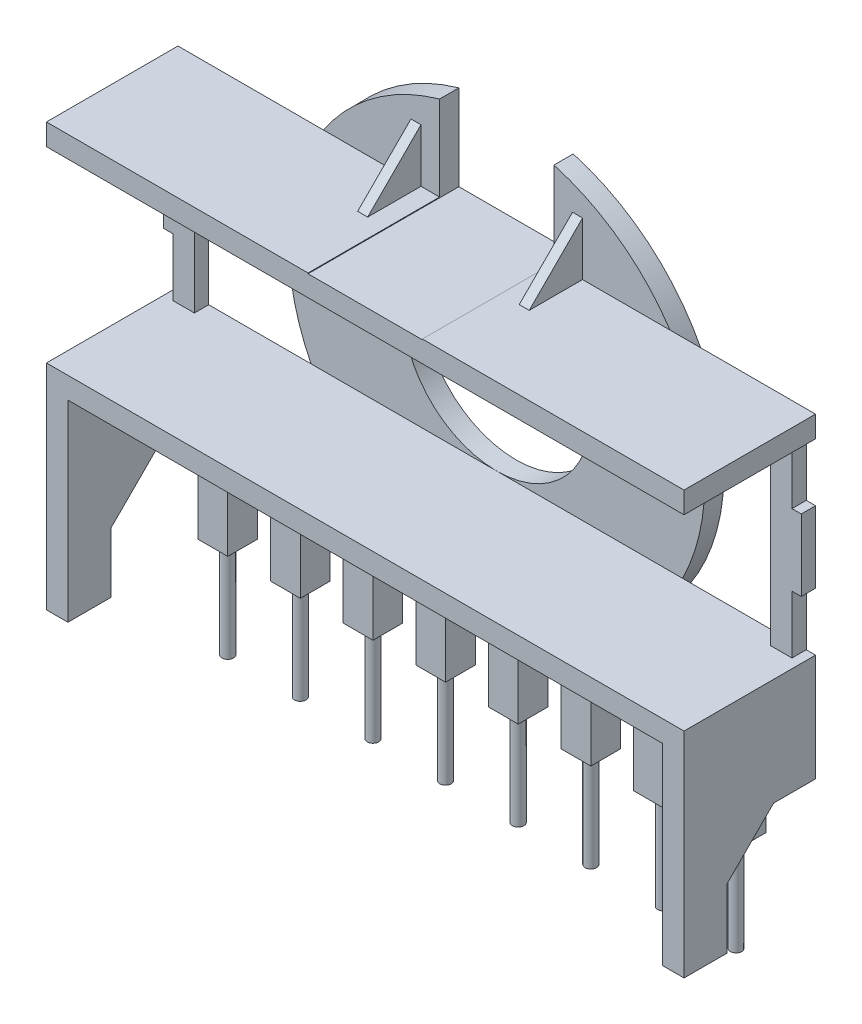
SolidWorks part; units mm, degrees
ref_plane "Front Plane" through (0, 0, 0) normal (0, 0, 1) x (1, 0, 0)
ref_plane "Top Plane" through (0, 0, 0) normal (0, 1, 0) x (1, 0, 0)
ref_plane "Right Plane" through (0, 0, 0) normal (1, 0, 0) x (0, 0, -1)
sketch "Sketch1" plane through (0, 0, 0) normal (0, 0, 1) x (1, 0, 0)
  line L0 (-4, 8) -> (0, 8)
  line L1 (0, 8) -> (4, 8)
  line L2 (4, 8) -> (4, 13.9894)
  line L3 (-4, 8) -> (-4, 13.9894)
  circle A0 centre (0, 0) radius 14.55
  circle A1 centre (0, 0) radius 6.55
  dimension "D1" = 29.1
  dimension "D2" = 13.1
  dimension "D3" = 8
  dimension "D4" = 8
extrude "Boss-Extrude1" add sketch "Sketch1" along normal blind 1.35 contours L3 A0 L2 L1 L0 A1
sketch "Sketch2" plane through (0, 0, 1.35) normal (0, 0, 1) x (1, 0, 0)
  line L1 (-22.3, 8.05) -> (22.3, 8.05)
  line L2 (-22.3, 8.05) -> (-22.3, 6.55)
  line L3 (-22.3, 6.55) -> (22.3, 6.55)
  line L4 (22.3, 8.05) -> (22.3, 6.55)
  line L5 (-22.3, 8.05) -> (22.3, 6.55) construction
  line L6 (-22.3, 6.55) -> (22.3, 8.05) construction
  line L7 (-22.3, -6.55) -> (22.3, -6.55)
  line L8 (-22.3, -6.55) -> (-22.3, -8.05)
  line L9 (-22.3, -8.05) -> (22.3, -8.05)
  line L10 (22.3, -6.55) -> (22.3, -8.05)
  line L11 (-22.3, -6.55) -> (22.3, -8.05) construction
  line L12 (-22.3, -8.05) -> (22.3, -6.55) construction
  line L13 (22.3, -8.05) -> (20.8, -8.05)
  line L14 (22.3, -8.05) -> (22.3, -21.5106)
  line L15 (22.3, -21.5106) -> (20.8, -21.5106)
  line L16 (20.8, -8.05) -> (20.8, -21.5106)
  line L17 (-22.3, -8.05) -> (-20.8, -8.05)
  line L18 (-22.3, -8.05) -> (-22.3, -21.5106)
  line L19 (-22.3, -21.5106) -> (-20.8, -21.5106)
  line L20 (-20.8, -8.05) -> (-20.8, -21.5106)
  line L21 (-5.3, 8.05) -> (-6, 8.05)
  line L22 (-5.3, 8.05) -> (-5.3, 11.7809)
  line L23 (-5.3, 11.7809) -> (-6, 11.7809)
  line L24 (-6, 8.05) -> (-6, 11.7809)
  line L25 (5.3, 8.05) -> (6, 8.05)
  line L26 (5.3, 8.05) -> (5.3, 11.7809)
  line L27 (5.3, 11.7809) -> (6, 11.7809)
  line L28 (6, 8.05) -> (6, 11.7809)
  circle A1 centre (0, 0) radius 6.55 construction
  point P0 (0, 7.3)
  point P5 (0, -7.3)
  line M2 (-4, 8) -> (-4, 13.9894)
  arc M3 (-4, 13.9894) -> (4, 13.9894) centre (0, 0) ccw
  line M4 (4, 13.9894) -> (4, 8)
  line M5 (4, 8) -> (-4, 8)
  dimension "D1" = 44.6
  dimension "D2" = 1.5
  dimension "D3" = 1.5
  dimension "D4" = 1.5
  dimension "D5" = 6
  dimension "D6" = 0.7
  dimension "D7" = 6
  dimension "D8" = 35.5
extrude "Boss-Extrude2" add sketch "Sketch2" along normal blind 9.2 contours L4 L1 L3 M3 | L1 L28 L27 L26 | L3 L1 M3 M4 M5 M2 | L2 L3 L1 M3 | L20 L9 L18 L19 | L8 L9 L7 M3 | L9 L7 M3 | L10 L7 L9 M3 | L14 L15 L16 L13 | L24 L23 L22 L21
sketch "Sketch3" plane through (0, 0, 1.35) normal (0, 0, 1) x (1, 0, 0)
  line L0 (-20.15, 6.55) -> (-20.15, -6.55)
  line L1 (-22.3, 6.55) -> (22.3, 6.55) construction
  line L2 (-22.3, -6.55) -> (22.3, -6.55) construction
  line L3 (21.65, 6.55) -> (21.65, -6.55)
  line L4 (-21.65, 6.55) -> (-21.65, -6.55)
  line L5 (20.15, 6.55) -> (20.15, -6.55)
  line L6 (-21.65, 6.55) -> (-20.15, 6.55)
  line L7 (20.15, 6.55) -> (21.65, 6.55)
  line L8 (20.15, -6.55) -> (21.65, -6.55)
  line L9 (-21.65, -6.55) -> (-20.15, -6.55)
  line L10 (-22.3, 2.5) -> (-22.3, -2.5)
  line L11 (22.3, 2.5) -> (22.3, -2.5)
  line L12 (-22.3, 2.5) -> (-21.65, 2.5)
  line L13 (-22.3, -2.5) -> (-21.65, -2.5)
  line L14 (22.3, 2.5) -> (21.65, 2.5)
  line L15 (22.3, -2.5) -> (21.65, -2.5)
  dimension "D1" = 40.3
  dimension "D2" = 20.15
  dimension "D3" = 1.5
  dimension "D4" = 1.5
  dimension "D5" = 44.6
  dimension "D6" = 22.3
  dimension "D7" = 5
  dimension "D8" = 2.5
  dimension "D9" = 5
extrude "Boss-Extrude3" add sketch "Sketch3" along normal blind 1 contours L4 L9 L0 L6 | L10 L13 L4 L12 | L15 L11 L14 L3 | L5 L8 L3 L7
sketch "Sketch5" plane through (6, 0, 0) normal (1, 0, 0) x (0, 0, -1)
  line L0 (-10.55, 8.05) -> (-5.0809, 8.05)
  line L1 (-10.55, 8.05) -> (-1.35, 8.05) construction
  line L2 (-5.0809, 8.05) -> (-1.35, 11.7809)
  line L3 (-1.35, 11.7809) -> (-10.55, 11.7809)
  line L4 (-10.55, 11.7809) -> (-10.55, 8.05)
  line L5 (-1.35, 8.05) -> (-1.35, 11.7809) construction
  dimension "D1" = 45
extrude "Cut-Extrude1" cut sketch "Sketch5" against normal through all
sketch "Sketch6" plane through (22.3, 0, 0) normal (1, 0, 0) x (0, 0, -1)
  line L0 (-7.55, -21.5106) -> (-7.55, -17.3175)
  line L1 (-10.55, -21.5106) -> (-1.35, -21.5106) construction
  line L2 (-7.55, -17.3175) -> (-4.2825, -14.05)
  line L3 (-4.2825, -14.05) -> (-1.35, -14.05)
  line L4 (-1.35, -6.55) -> (-1.35, -21.5106) construction
  line L5 (-1.35, -14.05) -> (-1.35, -21.5106)
  line L6 (-1.35, -21.5106) -> (-7.55, -21.5106)
  line L7 (-10.55, -6.55) -> (-1.35, -6.55) construction
  line L8 (-10.55, -6.55) -> (-10.55, -21.5106) construction
  dimension "D1" = 135
  dimension "D2" = 7.5
  dimension "D3" = 3
extrude "Cut-Extrude2" cut sketch "Sketch6" against normal through all
sketch "Sketch7" plane through (0, 0, 1.35) normal (0, 0, 1) x (1, 0, 0)
  line L1 (-20.8, -8.05) -> (20.8, -8.05)
  line L2 (-20.8, -8.05) -> (-20.8, -15.05)
  line L3 (-20.8, -15.05) -> (20.8, -15.05)
  line L4 (20.8, -8.05) -> (20.8, -15.05)
  dimension "D1" = 7
  dimension "D2" = 20.8
extrude "Boss-Extrude4" add sketch "Sketch7" along normal blind 0.5
sketch "Sketch8" plane through (0, -15.05, 0) normal (0, -1, 0) x (1, 0, 0)
  circle A0 centre (-17.78, 2.39) radius 0.4
  circle A1 centre (-12.7, 2.39) radius 0.4
  circle A2 centre (-7.62, 2.39) radius 0.4
  circle A3 centre (-2.54, 2.39) radius 0.4
  circle A4 centre (2.54, 2.39) radius 0.4
  circle A5 centre (7.62, 2.39) radius 0.4
  circle A6 centre (12.7, 2.39) radius 0.4
  circle A7 centre (17.78, 2.39) radius 0.4
  dimension "D2" = 0.8
  dimension "D1" = 2.39
  dimension "D3" = 2.54
  dimension "D4" = 5.08
  dimension "D5" = 5.08
  dimension "D6" = 5.08
  dimension "D7" = 5.08
  dimension "D8" = 5.08
  dimension "D9" = 5.08
  dimension "D10" = 5.08
extrude "Pins" add sketch "Sketch8" along normal blind 11 separate body
sketch "Sketch9" plane through (0, -8.05, 0) normal (0, -1, 0) x (1, 0, 0)
  line L0 (-12.9923, 1.35) -> (12.9923, 1.35) construction
  line L1 (-13.74, 3.43) -> (-11.66, 3.43)
  line L2 (-13.74, 3.43) -> (-13.74, 1.35)
  line L3 (-13.74, 1.35) -> (-11.66, 1.35)
  line L4 (-11.66, 3.43) -> (-11.66, 1.35)
  line L5 (-13.74, 3.43) -> (-11.66, 1.35) construction
  line L6 (-13.74, 1.35) -> (-11.66, 3.43) construction
  line L7 (-20.8, 1.35) -> (20.8, 1.35) construction
  line L8 (-18.82, 3.43) -> (-16.74, 3.43)
  line L9 (-18.82, 3.43) -> (-18.82, 1.35)
  line L10 (-18.82, 1.35) -> (-16.74, 1.35)
  line L11 (-16.74, 3.43) -> (-16.74, 1.35)
  line L12 (-18.82, 3.43) -> (-16.74, 1.35) construction
  line L13 (-18.82, 1.35) -> (-16.74, 3.43) construction
  line L15 (-8.66, 3.43) -> (-6.58, 3.43)
  line L16 (-8.66, 3.43) -> (-8.66, 1.35)
  line L17 (-8.66, 1.35) -> (-6.58, 1.35)
  line L18 (-6.58, 3.43) -> (-6.58, 1.35)
  line L19 (-8.66, 3.43) -> (-6.58, 1.35) construction
  line L20 (-8.66, 1.35) -> (-6.58, 3.43) construction
  line L21 (-3.58, 3.43) -> (-1.5, 3.43)
  line L22 (-3.58, 3.43) -> (-3.58, 1.35)
  line L23 (-3.58, 1.35) -> (-1.5, 1.35)
  line L24 (-1.5, 3.43) -> (-1.5, 1.35)
  line L25 (-3.58, 3.43) -> (-1.5, 1.35) construction
  line L26 (-3.58, 1.35) -> (-1.5, 3.43) construction
  line L27 (1.5, 3.43) -> (3.58, 3.43)
  line L28 (1.5, 3.43) -> (1.5, 1.35)
  line L29 (1.5, 1.35) -> (3.58, 1.35)
  line L30 (3.58, 3.43) -> (3.58, 1.35)
  line L31 (1.5, 3.43) -> (3.58, 1.35) construction
  line L32 (1.5, 1.35) -> (3.58, 3.43) construction
  line L33 (6.58, 3.43) -> (8.66, 3.43)
  line L34 (6.58, 3.43) -> (6.58, 1.35)
  line L35 (6.58, 1.35) -> (8.66, 1.35)
  line L36 (8.66, 3.43) -> (8.66, 1.35)
  line L37 (6.58, 3.43) -> (8.66, 1.35) construction
  line L38 (6.58, 1.35) -> (8.66, 3.43) construction
  line L39 (11.66, 3.43) -> (13.74, 3.43)
  line L40 (11.66, 3.43) -> (11.66, 1.35)
  line L41 (11.66, 1.35) -> (13.74, 1.35)
  line L42 (13.74, 3.43) -> (13.74, 1.35)
  line L43 (11.66, 3.43) -> (13.74, 1.35) construction
  line L44 (11.66, 1.35) -> (13.74, 3.43) construction
  line L45 (16.74, 3.43) -> (18.82, 3.43)
  line L46 (16.74, 3.43) -> (16.74, 1.35)
  line L47 (16.74, 1.35) -> (18.82, 1.35)
  line L48 (18.82, 3.43) -> (18.82, 1.35)
  line L49 (16.74, 3.43) -> (18.82, 1.35) construction
  line L50 (16.74, 1.35) -> (18.82, 3.43) construction
  point P0 (-12.7, 2.39)
  point P8 (-17.78, 2.39)
  point P16 (-7.62, 2.39)
  point P22 (-2.54, 2.39)
  point P28 (2.54, 2.39)
  point P34 (7.62, 2.39)
  point P40 (12.7, 2.39)
  point P46 (17.78, 2.39)
extrude "Boss-Extrude6" add sketch "Sketch9" along normal blind 11
